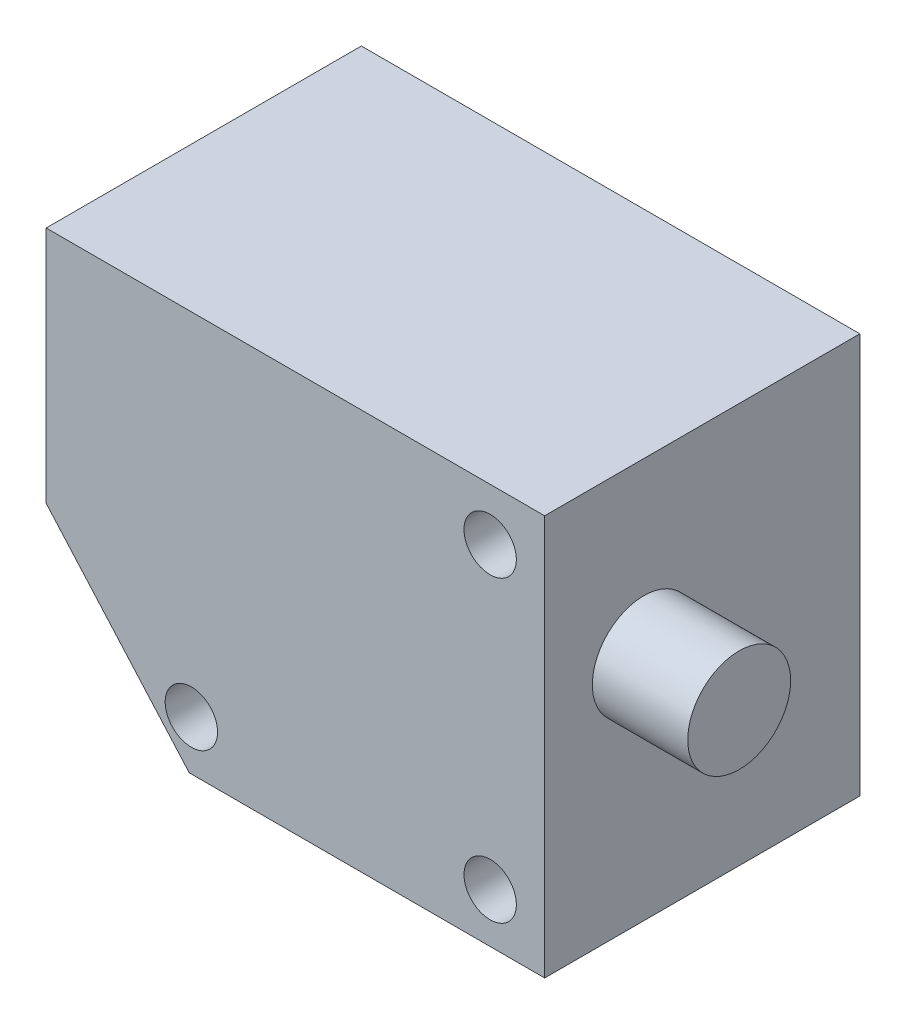
SolidWorks part; units mm, degrees
ref_plane "Plano frontal" through (0, 0, 0) normal (0, 0, 1) x (1, 0, 0)
ref_plane "Plano superior" through (0, 0, 0) normal (0, 1, 0) x (1, 0, 0)
ref_plane "Plano direito" through (0, 0, 0) normal (1, 0, 0) x (0, 0, -1)
sketch "Esboço1" plane through (0, 0, 0) normal (0, 1, 0) x (1, 0, 0)
  line L1 (-26.65, -16.85) -> (26.65, -16.85)
  line L2 (-26.65, -16.85) -> (-26.65, 16.85)
  line L3 (-26.65, 16.85) -> (26.65, 16.85)
  line L4 (26.65, -16.85) -> (26.65, 16.85)
  line L5 (0, 16.85) -> (0, -16.85) construction
  line L6 (-26.65, 0) -> (26.65, 0) construction
  point P0 (0, 0)
  dimension "D1" = 33.7
  dimension "D2" = 53.3
extrude "Ressalto-extrusão1" add sketch "Esboço1" along normal mid plane 42.8
sketch "Esboço2" plane through (0, 0, 16.85) normal (0, 0, 1) x (1, 0, 0)
  line L0 (-26.65, -21.4) -> (26.65, -21.4) construction
  line L1 (-26.65, -21.4) -> (-11.35, -21.4)
  line L2 (-26.65, 21.4) -> (-26.65, -21.4) construction
  line L3 (-26.65, -4.0934) -> (-26.65, -21.4)
  line L4 (-26.65, -4.0934) -> (-11.35, -21.4)
  line L5 (26.65, 21.4) -> (26.65, -21.4) construction
  dimension "D1" = 23.1
  dimension "D2" = 38
extrude "Corte-extrusão1" cut sketch "Esboço2" against normal through all
sketch "Esboço3" plane through (26.65, 0, 0) normal (1, 0, 0) x (0, 0, -1)
  line L0 (-16.85, -21.4) -> (16.85, -21.4) construction
  line L1 (-16.85, 21.4) -> (-16.85, -21.4) construction
  circle A0 centre (-6.25, 3.2) radius 5.5
  dimension "D1" = 11
  dimension "D2" = 24.6
  dimension "D3" = 10.6
extrude "Ressalto-extrusão2" add sketch "Esboço3" along normal blind 10.2
sketch "Esboço4" plane through (-26.65, 0, 0) normal (-1, 0, 0) x (0, 0, 1)
  circle A0 centre (6.25, 3.2) radius 5.5 construction
  circle A1 centre (6.25, 3.2) radius 5.5
extrude "Ressalto-extrusão3" add sketch "Esboço4" along normal blind 4
hole_wizard "Rebaixo para parafuso de máquina com cabeça panela de M31" positions "Esboço6" profile "Esboço8" counterbore size "M3" standard "Ansi Metric" end condition through all
sketch "Esboço6" plane through (0, 0, 16.85) normal (0, 0, 1) x (1, 0, 0)
  line L2 (-26.65, 21.4) -> (-26.65, -4.0934) construction
  line L3 (-11.35, -21.4) -> (26.65, -21.4) construction
  point P0 (20.825, 15.825)
  point P2 (20.825, -16.125)
  point P4 (-11.125, -16.125)
  point P5 (20.7731, 16.2888)
  point P7 (0, 0)
  point P8 (20.5996, -15.6607)
  point P10 (-11.3499, -15.4872)
  point P17 (20.825, 15.825)
  point P19 (20.825, -16.125)
  point P21 (-11.125, -16.125)
  dimension "D1" = 15.525
  dimension "D2" = 47.475
  dimension "D3" = 5.275
  dimension "D4" = 37.225
sketch "Esboço8" plane through (20.825, 15.825, 16.85) normal (1, 0, 0) x (0, -1, 0)
  line L0 (0, 0) -> (0, 33.7)
  line L1 (0, 33.7) -> (1.45, 33.7)
  line L3 (1.45, 33.7) -> (1.45, 4.39)
  line L4 (1.45, 4.39) -> (2.8, 4.39)
  line L5 (2.8, 4.39) -> (2.8, 0)
  line L7 (2.8, 0) -> (0, 0)
  line L11 (0, -6.35) -> (0, 107.95) construction
  dimension "Thru Hole Dia." = 2.9
  dimension "Thru Hole Depth" = 33.7
  dimension "C'Bore Dia." = 5.6
  dimension "C'Bore Depth" = 4.39
